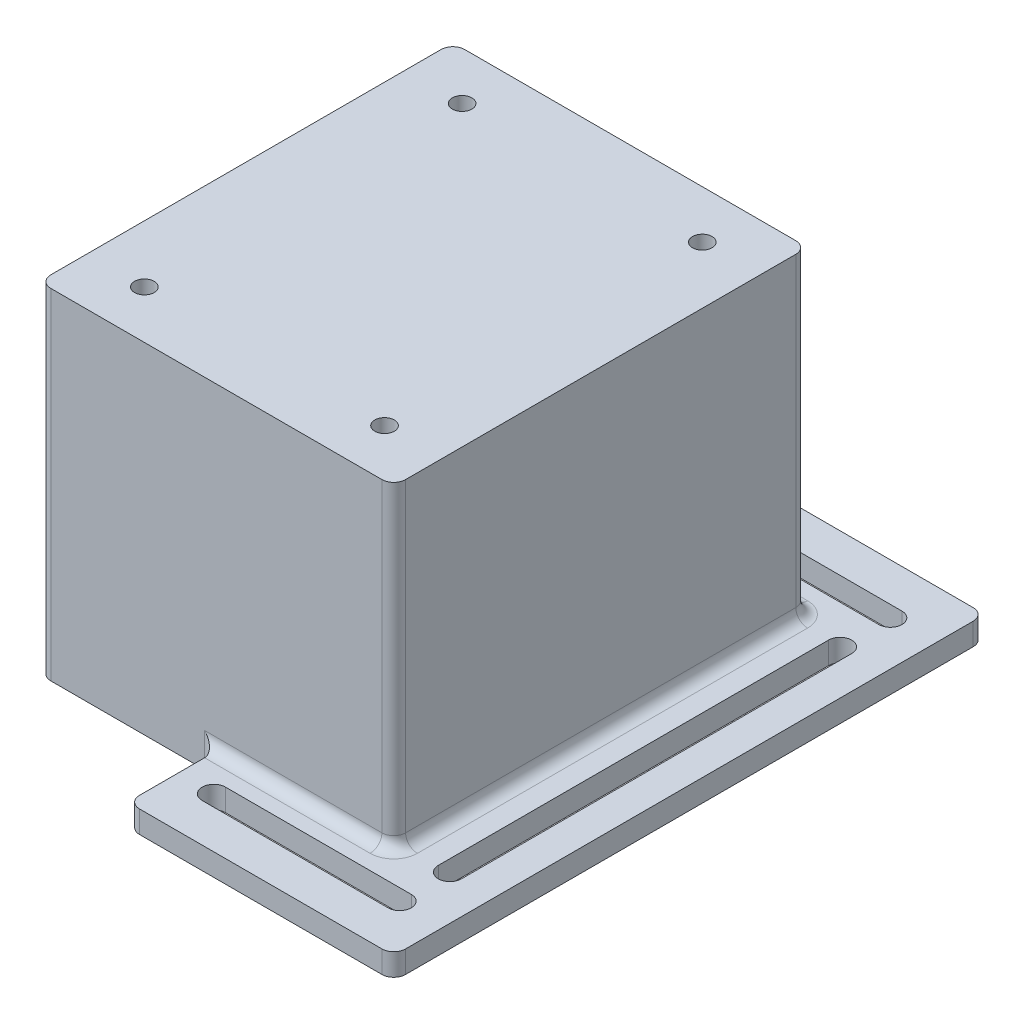
SolidWorks part; units mm, degrees
ref_plane "Front Plane" through (0, 0, 0) normal (0, 0, 1) x (1, 0, 0)
ref_plane "Top Plane" through (0, 0, 0) normal (0, 1, 0) x (1, 0, 0)
ref_plane "Right Plane" through (0, 0, 0) normal (1, 0, 0) x (0, 0, -1)
sketch "Sketch1" plane through (0, 0, 0) normal (0, 1, 0) x (1, 0, 0)
  line L1 (0, 0) -> (76.2, 0)
  line L2 (0, 0) -> (0, 88.9)
  line L3 (0, 88.9) -> (76.2, 88.9)
  line L4 (76.2, 0) -> (76.2, 88.9)
  dimension "D1" = 88.9
  dimension "D2" = 76.2
extrude "Boss-Extrude1" add sketch "Sketch1" along normal blind 73.025
sketch "Sketch2" plane through (0, 0, 0) normal (0, -1, 0) x (1, 0, 0)
  line L0 (38.1, 0) -> (38.1, 19.05)
  line L1 (0, 0) -> (76.2, 0) construction
  line L2 (38.1, 19.05) -> (95.25, 19.05)
  line L3 (38.1, -88.9) -> (38.1, -107.95)
  line L4 (38.1, 0) -> (38.1, -88.9)
  line L5 (76.2, -88.9) -> (0, -88.9) construction
  line L6 (38.1, -107.95) -> (95.25, -107.95)
  line L7 (95.25, 19.05) -> (95.25, -107.95)
  dimension "D1" = 38.1
  dimension "D2" = 19.05
  dimension "D3" = 19.05
  dimension "D4" = 19.05
  dimension "D5" = 19.05
extrude "Boss-Extrude2" add sketch "Sketch2" against normal blind 4.7625
fillet "Fillet1" radius 2.54 8 edges at (0, 36.5125, -88.9) (38.1, 2.3813, -107.95) (76.2, 38.8937, -88.9) (95.25, 2.3813, -107.95) (0, 36.5125, 0) (76.2, 38.8937, 0) (95.25, 2.3813, 19.05) (38.1, 2.3813, 19.05)
sketch "Sketch3" plane through (0, 4.7625, 0) normal (0, 1, 0) x (1, 0, 0)
  line L0 (38.1, 97.155) -> (95.25, 97.155) construction
  line L1 (38.1, 88.9) -> (38.1, 105.41) construction
  line L2 (95.25, 105.41) -> (95.25, -16.51) construction
  line L3 (0, 44.45) -> (95.25, 44.45) construction
  line L4 (0, 86.36) -> (0, 2.54) construction
  line L5 (76.2, 86.36) -> (95.25, 86.36) construction
  line L6 (76.2, 86.36) -> (76.2, 2.54) construction
  line L7 (76.2, 2.54) -> (76.2, 86.36) construction
  line L8 (85.725, 86.36) -> (85.725, 44.45) construction
  line L9 (45.7969, 99.655) -> (85.725, 99.655)
  line L10 (45.7969, 94.655) -> (85.725, 94.655)
  line L11 (45.7969, -10.755) -> (85.725, -10.755)
  line L12 (45.7969, -5.755) -> (85.725, -5.755)
  line L13 (88.225, 86.36) -> (88.225, 2.54)
  line L14 (83.225, 86.36) -> (83.225, 2.54)
  arc A0 (45.7969, 99.655) -> (45.7969, 94.655) centre (45.7969, 97.155) ccw
  arc A1 (85.725, 94.655) -> (85.725, 99.655) centre (85.725, 97.155) ccw
  arc A2 (45.7969, -10.755) -> (45.7969, -5.755) centre (45.7969, -8.255) cw
  arc A3 (85.725, -5.755) -> (85.725, -10.755) centre (85.725, -8.255) cw
  arc A4 (88.225, 86.36) -> (83.225, 86.36) centre (85.725, 86.36) ccw
  arc A5 (88.225, 2.54) -> (83.225, 2.54) centre (85.725, 2.54) cw
  point P32 (83.225, 44.45)
  point P37 (88.225, 44.45)
extrude "Cut-Extrude1" cut sketch "Sketch3" against normal through all
fillet "Fillet2" radius 2.54 7 edges at (55.88, 4.7625, -88.9) (75.4561, 4.7625, -88.1561) (76.2, 4.7625, -44.45) (75.4561, 4.7625, -0.7439) (38.1, 2.3813, -88.9) (55.88, 4.7625, 0) (38.1, 2.3813, 0)
sketch "Sketch4" plane through (0, 73.025, 0) normal (0, 1, 0) x (1, 0, 0)
  line L0 (12.3031, 88.9) -> (12.3031, 0) construction
  line L1 (73.66, 88.9) -> (2.54, 88.9) construction
  line L2 (2.54, 0) -> (73.66, 0) construction
  line L3 (0, 44.45) -> (76.2, 44.45) construction
  line L4 (0, 86.36) -> (0, 2.54) construction
  line L5 (76.2, 2.54) -> (76.2, 86.36) construction
  line L6 (38.1, 88.9) -> (38.1, 0) construction
  circle A0 centre (12.3031, 78.5812) radius 2.1
  circle A1 centre (12.3031, 10.3188) radius 2.1
  circle A2 centre (63.8969, 10.3188) radius 2.1
  circle A3 centre (63.8969, 78.5812) radius 2.1
  dimension "D2" = 34.1313
  dimension "D1" = 12.3031
extrude "Cut-Extrude2" cut sketch "Sketch4" against normal blind 25.4
